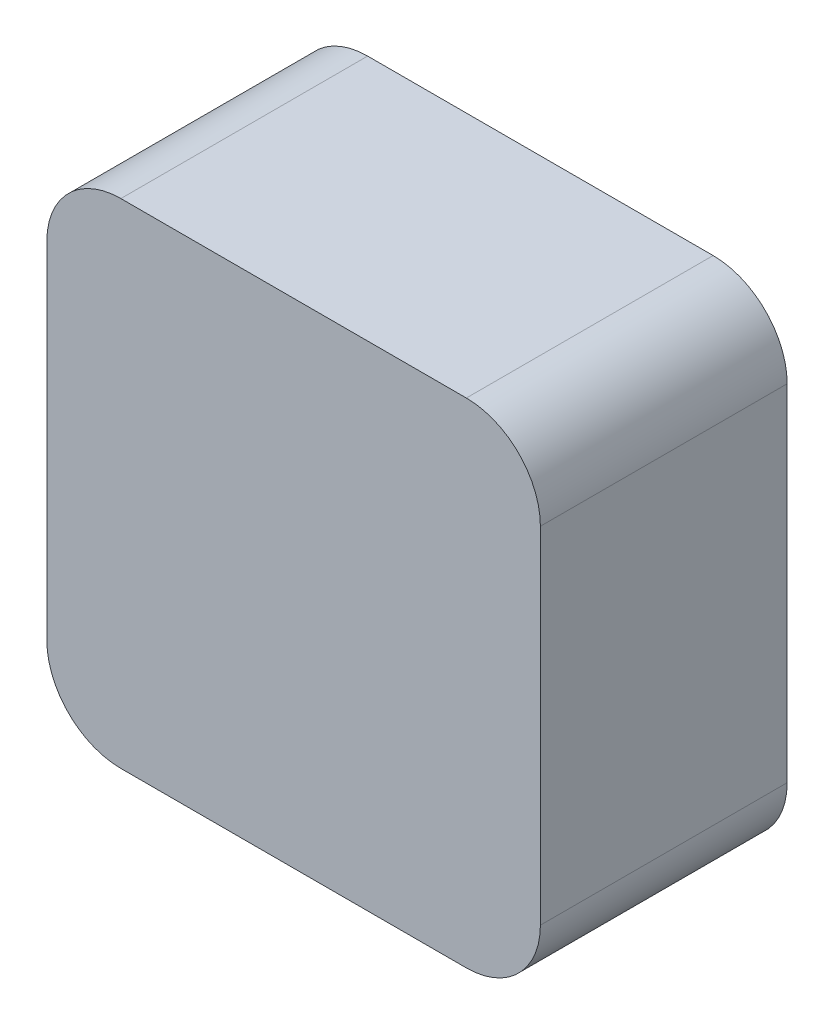
SolidWorks part; units mm, degrees
ref_plane "Front Plane" through (0, 0, 0) normal (0, 0, 1) x (1, 0, 0)
ref_plane "Top Plane" through (0, 0, 0) normal (0, 1, 0) x (1, 0, 0)
ref_plane "Right Plane" through (0, 0, 0) normal (1, 0, 0) x (0, 0, -1)
sketch "Sketch1" plane through (0, 0, 0) normal (0, 0, 1) x (1, 0, 0)
  line L1 (-145, 160.5) -> (-135, 160.5)
  line L2 (-145, 160.5) -> (-145, 150.5)
  line L3 (-145, 150.5) -> (-135, 150.5)
  line L4 (-135, 160.5) -> (-135, 150.5)
  circle A1 centre (-140, 155.5) radius 1.5
extrude "Boss-Extrude1" add sketch "Sketch1" along normal blind 5
fillet "Fillet1" radius 1.5 4 edges at (-145, 150.5, 2.5) (-145, 160.5, 2.5) (-135, 160.5, 2.5) (-135, 150.5, 2.5)
sketch "Sketch2" plane through (0, 0, 5) normal (0, 0, 1) x (1, 0, 0)
  circle A0 centre (-140, 155.5) radius 1.6
extrude "Boss-Extrude2" add sketch "Sketch2" against normal blind 1
sketch "Sketch3" plane through (0, 0, 0) normal (0, 0, -1) x (-1, 0, 0)
  circle A0 centre (140, 155.5) radius 2.25
extrude "Cut-Extrude1" cut sketch "Sketch3" against normal blind 4
